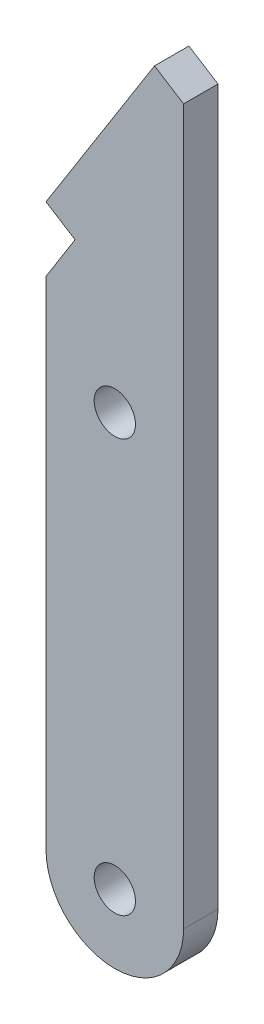
SolidWorks part; units mm, degrees
ref_plane "Alzado" through (0, 0, 0) normal (0, 0, 1) x (1, 0, 0)
ref_plane "Planta" through (0, 0, 0) normal (0, 1, 0) x (1, 0, 0)
ref_plane "Vista lateral" through (0, 0, 0) normal (1, 0, 0) x (0, 0, -1)
sketch "Croquis1" plane through (0, 0, 0) normal (0, 0, 1) x (1, 0, 0)
  line L0 (0, 0) -> (0, 70) construction
  line L1 (-5, 36.0807) -> (-5, 0)
  line L2 (5, 51.9286) -> (5, 0)
  line L3 (5, 70) -> (14.7542, 70) construction
  line L4 (14.7542, 70) -> (14.7542, 30) construction
  line L5 (14.7542, 30) -> (0, 30) construction
  line L6 (-24.5438, -4.7544) -> (-44.799, 0.7887) construction
  line L7 (-34.6714, -1.9828) -> (-18.1441, 58.4097) construction
  line L8 (2.8857, 53.2627) -> (-5, 40.7655)
  line L9 (-5, 40.7655) -> (5, 40.7655) construction
  line L10 (-5, 40.7655) -> (-2.8857, 39.4314) construction
  line L11 (-2.8857, 39.4314) -> (5, 51.9286) construction
  line L12 (5, 51.9286) -> (2.8857, 53.2627)
  line L13 (-2.8857, 39.4314) -> (-5, 36.0807) construction
  line L14 (-5, 40.7655) -> (-2.8857, 39.4314)
  line L15 (-2.8857, 39.4314) -> (-5, 36.0807)
  circle A0 centre (0, 0) radius 1.5
  circle A1 centre (0, 70) radius 1.5 construction
  arc A2 (-5, 0) -> (5, 0) centre (0, 0) ccw
  arc A3 (5, 70) -> (-5, 70) centre (0, 70) ccw construction
  circle A4 centre (0, 30) radius 1.5
  dimension "D2" = 14.7772
  dimension "D1" = 70
extrude "Saliente-Extruir1" add sketch "Croquis1" along normal blind 2.5
